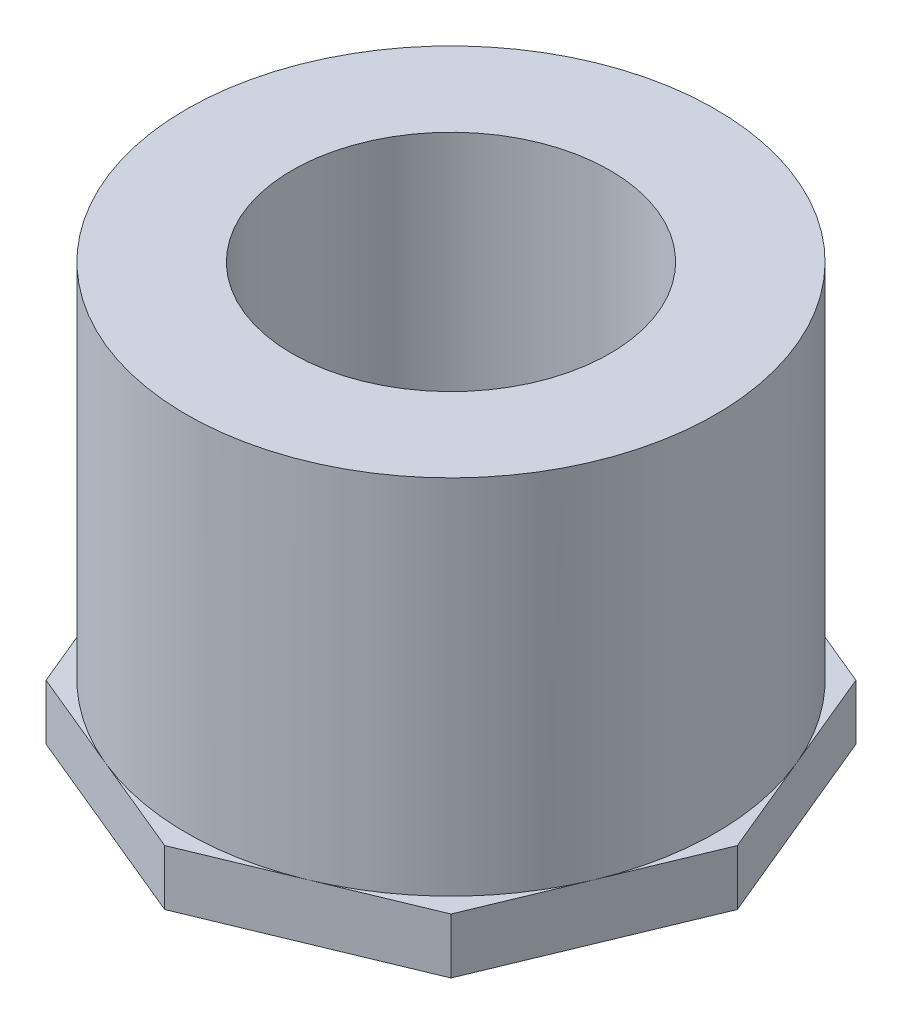
SolidWorks part; units mm, degrees
ref_plane "Front" through (0, 0, 0) normal (0, 0, 1) x (1, 0, 0)
ref_plane "Top" through (0, 0, 0) normal (0, 1, 0) x (1, 0, 0)
ref_plane "Right" through (0, 0, 0) normal (1, 0, 0) x (0, 0, -1)
sketch "Sketch1" plane through (0, 0, 0) normal (0, 0, 1) x (1, 0, 0)
  line L0 (-6.35, 0) -> (-6.35, 38.1)
  line L1 (-6.35, 38.1) -> (-24.13, 38.1)
  line L2 (-24.13, 38.1) -> (-24.13, 0)
  line L5 (-24.13, 0) -> (-6.35, 0)
  line L6 (0, 0) -> (0, -9.8334) construction
  point P5 (0, 0)
  dimension "D1" = 48.26
  dimension "D2" = 12.7
  dimension "D3" = 38.1
revolve "Revolve1" add sketch "Sketch1" angle 360 about L6
sketch "Sketch2" plane through (0, 0, 0) normal (0, -1, 0) x (1, 0, 0)
  line L1 (0, 26.1181) -> (-18.4683, 18.4683)
  line L2 (-18.4683, 18.4683) -> (-26.1181, 0)
  line L3 (-26.1181, 0) -> (-18.4683, -18.4683)
  line L4 (-18.4683, -18.4683) -> (0, -26.1181)
  line L5 (0, -26.1181) -> (18.4683, -18.4683)
  line L6 (18.4683, -18.4683) -> (26.1181, 0)
  line L7 (26.1181, 0) -> (18.4683, 18.4683)
  line L8 (18.4683, 18.4683) -> (0, 26.1181)
  circle A0 centre (0, 0) radius 24.13 construction
  circle A1 centre (0, 0) radius 24.13 construction
  circle A2 centre (0, 0) radius 6.35 construction
  circle A3 centre (0, 0) radius 6.35
  point P1 (0, 0)
extrude "Boss-Extrude1" add sketch "Sketch2" against normal blind 5.0546
hole_wizard "1 NPT Tapped Hole1" positions "Sketch3" profile "Sketch4" size "1" standard "ANSI Inch" end condition through all
sketch "Sketch3" plane through (0, 0, 0) normal (0, -1, 0) x (-1, 0, 0)
  point P3 (0, 0)
  point P7 (0, 0)
sketch "Sketch4" plane through (0, 0, 0) normal (1, 0, 0) x (0, 0, -1)
  line L0 (0, 0) -> (0, 38.1)
  line L1 (0, 38.1) -> (14.4907, 38.1)
  line L2 (-15.228, 16.7869) -> (-15.7306, 0) construction
  line L3 (14.4907, 38.1) -> (14.4907, 16.7869)
  line L4 (14.4907, 16.7869) -> (15.228, 16.7869)
  line L5 (15.228, 16.7869) -> (15.7306, 0)
  line L7 (15.7306, 0) -> (0, 0)
  line L8 (0, -6.35) -> (0, 107.95) construction
  line L11 (-14.4907, 16.7869) -> (-15.228, 16.7869) construction
  dimension "Thru Tap Drill Dia." = 28.9814
  dimension "Thru Tap Drill Depth" = 38.1
  dimension "Thread Dia." = 31.4612
  dimension "Thread Angle" = 3.43
  dimension "Thread Depth" = 16.7869
cosmetic thread "Hole Thread1" parameters "D1"=16.7869, "D2"=33.401
